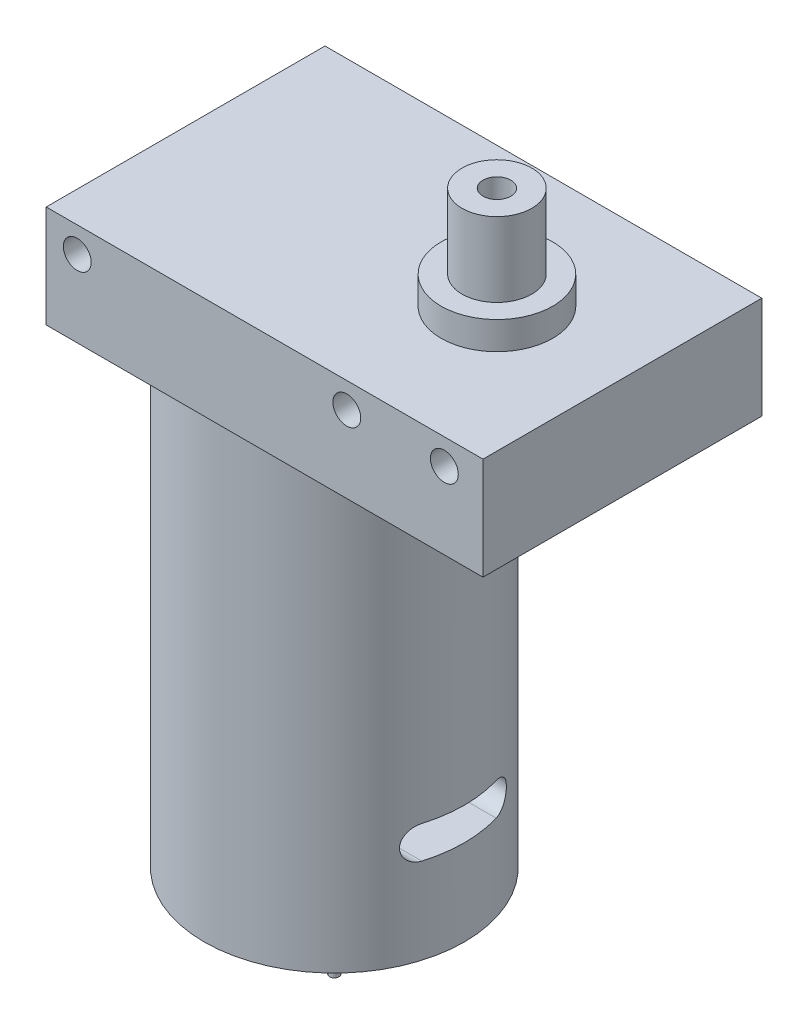
SolidWorks part; units mm, degrees
material "商用纯 CP-Ti UNS R50400 (SS)"
ref_plane "前视基准面" through (0, 0, 0) normal (0, 0, 1) x (1, 0, 0)
ref_plane "上视基准面" through (0, 0, 0) normal (0, 1, 0) x (1, 0, 0)
ref_plane "右视基准面" through (0, 0, 0) normal (1, 0, 0) x (0, 0, -1)
sketch "草图1" plane through (0, 0, 0) normal (0, 1, 0) x (1, 0, 0)
  line L1 (0, 0) -> (47, 0)
  line L2 (0, 0) -> (0, -30)
  line L3 (0, -30) -> (47, -30)
  line L4 (47, 0) -> (47, -30)
  dimension "D1" = 47
  dimension "D2" = 30
extrude "凸台-拉伸1" add sketch "草图1" along normal blind 11
sketch "草图2" plane through (0, 11, 0) normal (0, 1, 0) x (1, 0, 0)
  line L0 (47, 0) -> (0, 0) construction
  line L1 (47, -30) -> (47, 0) construction
  circle A0 centre (33.5, -15) radius 6
  dimension "D1" = 15
  dimension "D3" = 12
  dimension "D2" = 13.5
extrude "凸台-拉伸2" add sketch "草图2" along normal blind 3
sketch "草图3" plane through (0, 14, 0) normal (0, 1, 0) x (1, 0, 0)
  line L1 (37.2528, -15) -> (35.3764, -11.75) construction
  line L2 (35.3764, -11.75) -> (31.6236, -11.75) construction
  line L3 (31.6236, -11.75) -> (29.7472, -15) construction
  line L4 (29.7472, -15) -> (31.6236, -18.25) construction
  line L5 (31.6236, -18.25) -> (35.3764, -18.25) construction
  line L6 (35.3764, -18.25) -> (37.2528, -15) construction
  circle A0 centre (33.5, -15) radius 3.25 construction
  circle A1 centre (33.5, -15) radius 3.7528
  dimension "D1" = 6.5
extrude "凸台-拉伸3" add sketch "草图3" along normal blind 8
sketch "草图4" plane through (0, 0, 0) normal (0, -1, 0) x (1, 0, 0)
  line L0 (0, 30) -> (47, 30) construction
  line L1 (0, 0) -> (0, 30) construction
  circle A0 centre (16, 15) radius 14
  dimension "D1" = 15
  dimension "D3" = 28
  dimension "D2" = 16
extrude "凸台-拉伸4" add sketch "草图4" along normal blind 50
sketch "草图5" plane through (0, -50, 0) normal (0, -1, 0) x (1, 0, 0)
  circle A0 centre (16, 15) radius 5
  dimension "D1" = 10
extrude "凸台-拉伸5" add sketch "草图5" along normal blind 2
sketch "草图6" plane through (0, 0, 30) normal (0, 0, 1) x (1, 0, 0)
  line L0 (0, 11) -> (47, 11) construction
  circle A0 centre (3.3408, 8.25) radius 1.5
  circle A1 centre (32.3408, 8.25) radius 1.5
  circle A2 centre (42.8408, 8.25) radius 1.5
  dimension "D1" = 3
  dimension "D2" = 39.5
  dimension "D3" = 10.5
  dimension "D4" = 2.75
extrude "切除-拉伸1" cut sketch "草图6" against normal through all
sketch "草图7" plane through (0, 0, 0) normal (-1, 0, 0) x (0, 0, 1)
  line L0 (15, 11) -> (15, -39) construction
  line L1 (0, 11) -> (30, 11) construction
  line L2 (-10.279, -39) -> (39.7397, -39) construction
  line L3 (11, -39) -> (19, -39) construction
  line L4 (11, -37.25) -> (19, -37.25)
  line L5 (11, -40.75) -> (19, -40.75)
  arc A0 (11, -37.25) -> (11, -40.75) centre (11, -39) ccw
  arc A1 (19, -40.75) -> (19, -37.25) centre (19, -39) ccw
  point P8 (15, -39)
  dimension "D1" = 3.5
  dimension "D2" = 8
extrude "切除-拉伸2" cut sketch "草图7" against normal through all
sketch "草图9" plane through (0, 22, 0) normal (0, 1, 0) x (1, 0, 0)
  circle A0 centre (33.5, -15) radius 1.5
extrude "切除-拉伸3" cut sketch "草图9" against normal blind 8
sketch "草图11" plane through (0, -52, 0) normal (0, -1, 0) x (1, 0, 0)
  circle A0 centre (16, 15) radius 0.5
extrude "凸台-拉伸6" add sketch "草图11" along normal blind 8
